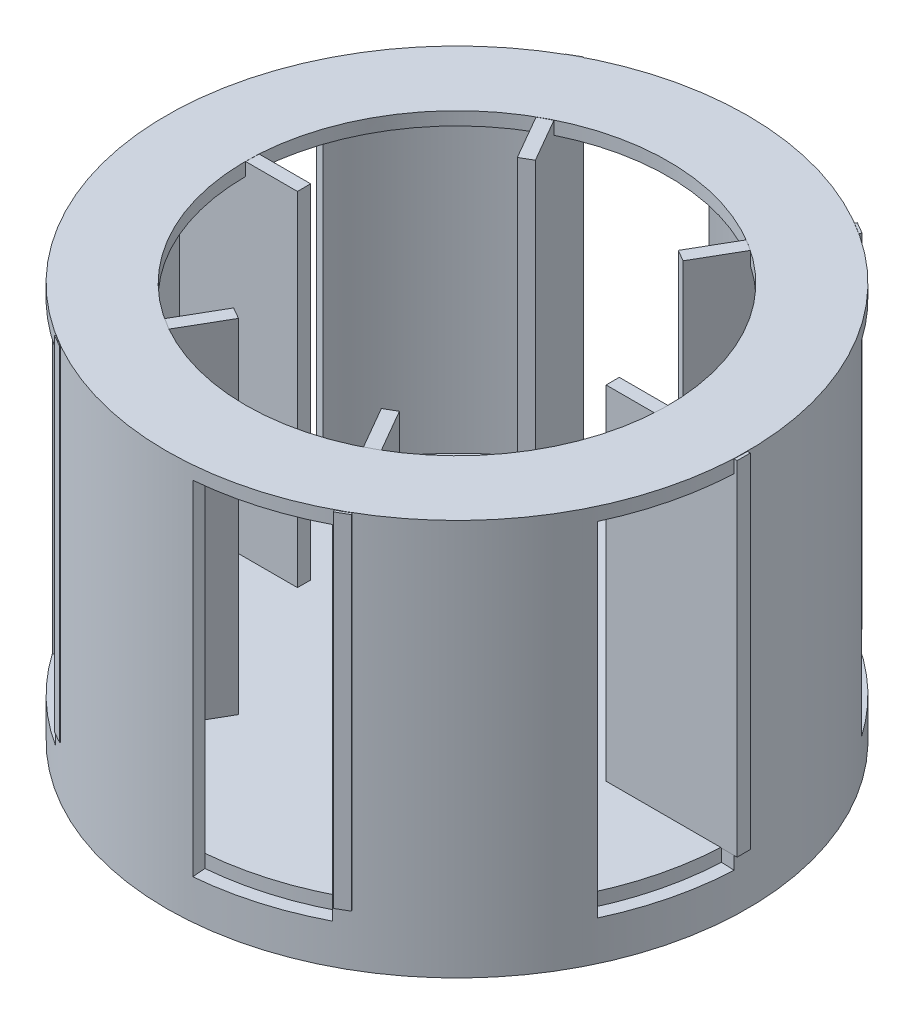
SolidWorks part; units mm, degrees
ref_plane "Front Plane" through (0, 0, 0) normal (0, 0, 1) x (1, 0, 0)
ref_plane "Top Plane" through (0, 0, 0) normal (0, 1, 0) x (1, 0, 0)
ref_plane "Right Plane" through (0, 0, 0) normal (1, 0, 0) x (0, 0, -1)
sketch "Sketch1" plane through (0, 0, 0) normal (0, 0, 1) x (1, 0, 0)
  line L0 (0, 0) -> (0, 13.346) construction
  line L7 (0, 0) -> (5.5, 0)
  line L8 (5.5, 0) -> (5.5, 7)
  line L9 (5.5, 7) -> (0, 7)
  line L10 (0, 0) -> (0, 7)
  dimension "D1" = 7
  dimension "D2" = 5.5
revolve "Revolve1" add sketch "Sketch1" angle 360 about L0
shell "Shell1" thickness 0.25
sketch "Sketch6" plane through (0, 7, 0) normal (0, 1, 0) x (1, 0, 0)
  circle A0 centre (0, 0) radius 5.5 construction
  circle A1 centre (0, 0) radius 5.5
  circle A2 centre (0, 0) radius 4
  dimension "D1" = 8
extrude "Boss-Extrude1" add sketch "Sketch6" against normal blind 0.25
sketch "Sketch7" plane through (0, 0, 0) normal (1, 0, 0) x (0, 0, -1)
  line L0 (0, -2.3271) -> (0, 10.1465) construction
  line L1 (4, 7) -> (-4, 7) construction
  line L2 (-2.4, 6.75) -> (-0.25, 6.75)
  line L3 (-2.4, 6.75) -> (-2.4, 0.25)
  line L4 (-2.4, 0.25) -> (-0.25, 0.25)
  line L5 (-0.25, 6.75) -> (-0.25, 0.25)
  dimension "D1" = 2.15
  dimension "D2" = 6.5
  dimension "D3" = 0.25
  dimension "D4" = 0.25
wrap "Wrap1" sketch "Sketch7" wrap type deboss source sketch "Sketch7" thickness 0.25 face at (0, 7, -5.5) parameters "D1"=0.25
pattern_circular "CirPattern1" count 6 over 360 about axis through (0, 0, 0) along (0, 1, 0) of "Wrap1"
sketch "Sketch10" plane through (0, 0, 0) normal (0, 0, 1) x (1, 0, 0)
  line L0 (-5.5, 7) -> (-5.5, 0) construction
  line L1 (-5.5, 6.995) -> (-3.02, 6.995)
  line L2 (-5.5, 6.995) -> (-5.5, 0.495)
  line L3 (-5.5, 0.495) -> (-3.02, 0.495)
  line L4 (-3.02, 6.995) -> (-3.02, 0.495)
  line L5 (-5.5, 0) -> (5.5, 0) construction
  dimension "D1" = 2.48
  dimension "D2" = 0.495
  dimension "D3" = 6.5
extrude "Boss-Extrude2" add sketch "Sketch10" against normal blind 0.25
pattern_circular "CirPattern2" count 6 over 360 about axis through (0.0268, 0, 0.0008) along (0, 1, 0) of "Boss-Extrude2"
sketch "Sketch11" plane through (0, 0, 0) normal (0, 0, 1) x (1, 0, 0)
  line L0 (-5.5, 0) -> (5.5, 0) construction
  line L1 (-5.5, 0) -> (0, 0)
  line L2 (-5.5, 0) -> (-5.5, -0.5)
  line L3 (-5.5, -0.5) -> (-1.5, -0.5)
  line L4 (-1.5, -0.5) -> (-1.5, -3)
  line L5 (-1.5, -3) -> (0, -3)
  line L6 (0, -3) -> (0, 0)
  dimension "D1" = 0.5
  dimension "D2" = 2.5
  dimension "D3" = 1.5
revolve "Revolve3" add sketch "Sketch11" angle 360 about L6
sketch "Sketch12" plane through (0, -3, 0) normal (0, -1, 0) x (1, 0, 0)
  circle A0 centre (0, 0) radius 0.75
  dimension "D1" = 1.5
extrude "Cut-Extrude1" cut sketch "Sketch12" against normal up to next
